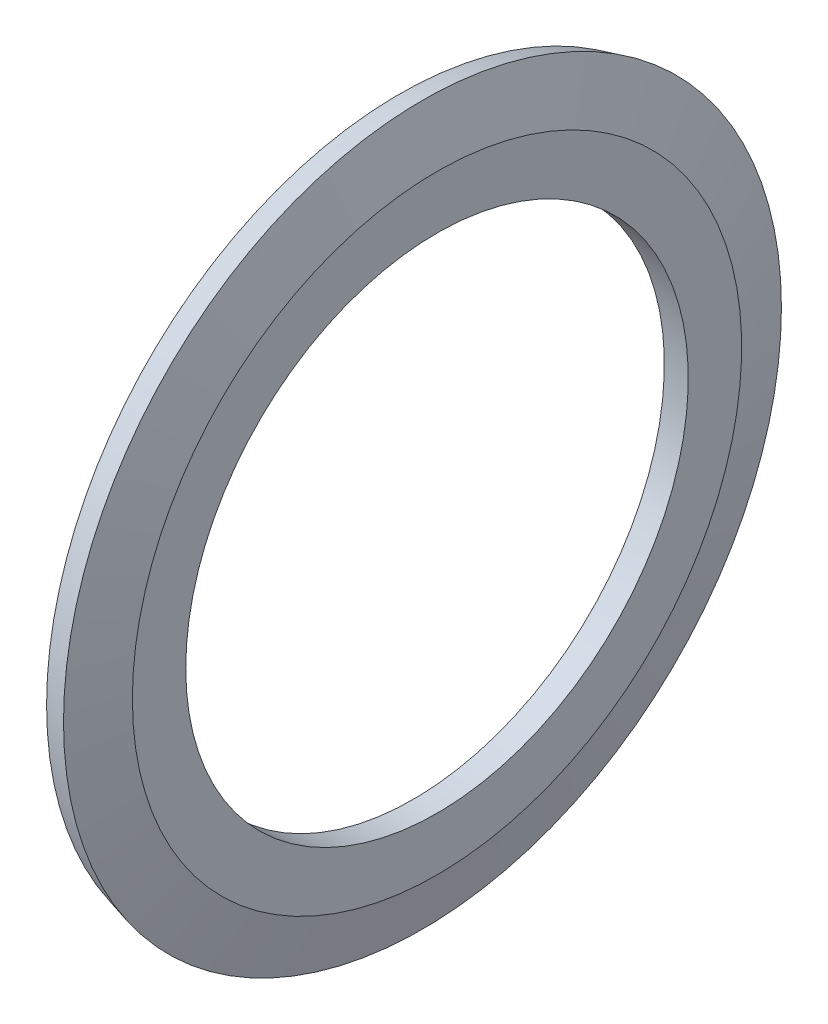
SolidWorks part; units mm, degrees
ref_plane "Front Plane" through (0, 0, 0) normal (0, 0, 1) x (1, 0, 0)
ref_plane "Top Plane" through (0, 0, 0) normal (0, 1, 0) x (1, 0, 0)
ref_plane "Right Plane" through (0, 0, 0) normal (1, 0, 0) x (0, 0, -1)
sketch "Sketch1" plane through (0, 0, 0) normal (0, 0, 1) x (1, 0, 0)
  line L0 (0, 0) -> (1, 0) construction
  line L1 (0, 10.5) -> (0, 12.5983)
  line L2 (0, 12.5983) -> (-0.5742, 14.7412)
  line L3 (1, 10.5) -> (1, 12.73)
  line L4 (1, 12.73) -> (0.3918, 15)
  line L5 (0, 10.5) -> (1, 10.5)
  line L6 (-0.5742, 14.7412) -> (0.3918, 15)
  dimension "E" = 21
  dimension "F" = 30
  dimension "MSM_15" = 1
  dimension "D2" = 15
  dimension "P.D." = 25.46
revolve "Revolve1" add sketch "Sketch1" angle 360 about L0
sketch "Sketch2" [suppressed] plane through (0, 0, 0) normal (0, 0, 1) x (1, 0, 0)
  line L0 (0, 0) -> (0.5753, 0) construction
  line L1 (0, 15.7833) -> (0, -15.7833) construction
  line L2 (0.5753, 17.5) -> (0.5753, -17.5) construction
  line L3 (1, -15.915) -> (1, 15.915) construction
  line L4 (-0.3906, 15.5) -> (1, 15.5)
  line L5 (-0.3906, 15.5) -> (-0.3906, 17.5)
  line L6 (-0.3906, 17.5) -> (1, 17.5)
  line L7 (1, 15.5) -> (1, 17.5)
  line L8 (-0.3906, 17.2412) -> (-0.3906, -17.2412) construction
  dimension "FC" = 31
revolve "Cut-Revolve1" [suppressed] cut sketch "Sketch2" angle 360 about L0
